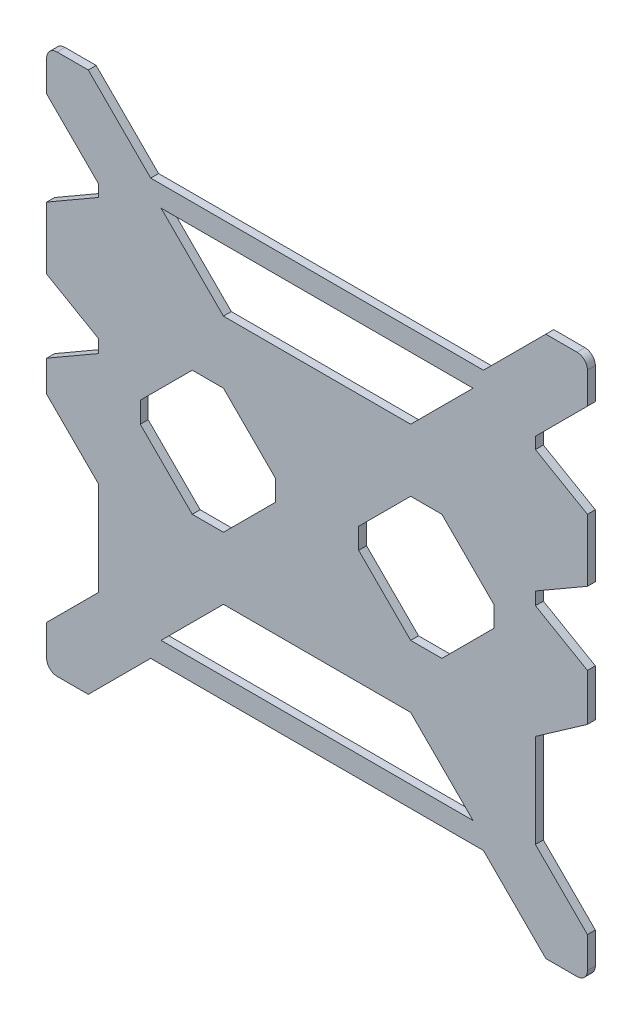
SolidWorks part; units mm, degrees
material "5052-H32"
ref_plane "Front Plane" through (0, 0, 0) normal (0, 0, 1) x (1, 0, 0)
ref_plane "Top Plane" through (0, 0, 0) normal (0, 1, 0) x (1, 0, 0)
ref_plane "Right Plane" through (0, 0, 0) normal (1, 0, 0) x (0, 0, -1)
sketch "Model" plane through (0, 0, 0) normal (0, 0, 1) x (1, 0, 0)
  line L0 (38.5361, 132.6139) -> (38.5361, 132.4727)
  line L1 (38.5361, -178.6774) -> (38.5361, -178.7219)
  line L2 (-253.5639, -197.5861) -> (-253.5639, -197.7273)
  line L3 (-290.6813, -31.2683) -> (-258.9313, -12.9374)
  line L4 (-258.9313, -82.0683) -> (-258.9313, -139.2183)
  line L5 (38.5361, 132.6139) -> (38.5361, 132.4727)
  line L6 (38.5361, -178.6774) -> (38.5361, -178.7219)
  line L7 (7.7687, -139.2183) -> (7.7687, -82.0683)
  line L8 (39.5187, -59.8367) -> (39.5187, -31.2683)
  line L9 (-23.9813, 95.7317) -> (-227.1813, 95.7317)
  line L10 (-290.6813, 108.4317) -> (-258.9313, 76.6817)
  line L11 (-30.3313, -145.5683) -> (-68.4313, -107.4683)
  line L12 (-23.9813, -158.2683) -> (14.1187, -196.3683)
  line L13 (39.5187, 108.4317) -> (39.5187, 127.4817)
  line L14 (-227.1813, 95.7317) -> (-265.2813, 133.8317)
  line L15 (-220.8313, 83.0317) -> (-182.7313, 44.9317)
  line L16 (-274.6813, -45.4288) -> (-254.6813, -45.4288) construction
  line L17 (39.5187, -170.9683) -> (7.7687, -139.2183)
  line L18 (-265.2813, -196.3683) -> (-227.1813, -158.2683)
  line L19 (-182.7313, -107.4683) -> (-68.4313, -107.4683)
  line L20 (-264.6813, -45.4288) -> (-264.6813, -43.5832) construction
  line L21 (7.7687, 76.6817) -> (39.5187, 108.4317)
  line L22 (-23.9813, 95.7317) -> (14.1187, 133.8317)
  line L23 (-30.3313, 83.0317) -> (-68.4313, 44.9317)
  line L24 (39.5187, -31.2683) -> (7.7687, -12.9374)
  line L25 (-258.9313, -139.2183) -> (-290.6813, -170.9683)
  line L26 (-182.7313, 44.9317) -> (-68.4313, 44.9317)
  line L27 (-220.8313, -145.5683) -> (-182.7313, -107.4683)
  line L28 (-220.8313, -145.5683) -> (-30.3313, -145.5683)
  line L29 (-258.9313, -82.0683) -> (-290.6813, -50.3183)
  line L30 (-290.6813, -31.2683) -> (-290.6813, -50.3183)
  line L31 (-274.6813, -43.9683) -> (-274.6813, -31.2683) construction
  line L32 (-258.9313, -12.9374) -> (-258.9313, -5.1492)
  line L33 (-201.7813, -69.3683) -> (-233.5313, -37.6183)
  line L34 (-182.7313, -69.3683) -> (-201.7813, -69.3683)
  line L35 (7.7687, -12.9374) -> (7.7687, -5.1492)
  line L36 (7.7687, -5.1492) -> (39.5187, 13.1817)
  line L37 (-150.9813, -37.6183) -> (-182.7313, -69.3683)
  line L38 (39.5187, -59.8367) -> (10.4646, -80.1806)
  line L39 (10.4646, -80.1806) -> (7.7687, -82.0683)
  line L40 (-100.1813, -37.6183) -> (-100.1813, -24.9183)
  line L41 (-150.9813, -37.6183) -> (-150.9813, -24.9183)
  line L42 (-150.9813, -24.9183) -> (-182.7313, 6.8317)
  line L43 (-182.7313, 6.8317) -> (-201.7813, 6.8317)
  line L44 (-201.7813, 6.8317) -> (-233.5313, -24.9183)
  line L45 (-233.5313, -24.9183) -> (-233.5313, -37.6183)
  line L46 (-17.6313, -24.9183) -> (-17.6313, -37.6183)
  line L47 (-49.3813, 6.8317) -> (-17.6313, -24.9183)
  line L48 (-220.8313, 83.0317) -> (-30.3313, 83.0317)
  line L49 (-68.4313, 6.8317) -> (-49.3813, 6.8317)
  line L50 (-100.1813, -24.9183) -> (-68.4313, 6.8317)
  line L51 (-100.1813, -37.6183) -> (-68.4313, -69.3683)
  line L52 (-68.4313, -69.3683) -> (-49.3813, -69.3683)
  line L53 (-49.3813, -69.3683) -> (-17.6313, -37.6183)
  line L54 (39.5187, 13.1817) -> (39.5187, 51.2817)
  line L55 (39.5187, 51.2817) -> (7.7687, 69.6126)
  line L56 (7.7687, 69.6126) -> (7.7687, 76.6817)
  line L57 (-258.9313, -5.1492) -> (-290.6813, 13.1817)
  line L58 (-265.2813, -196.3683) -> (-284.3313, -196.3683)
  line L59 (-290.6813, -190.0183) -> (-290.6813, -170.9683)
  line L60 (-290.6813, 108.4317) -> (-290.6813, 127.4817)
  line L61 (-284.3313, 133.8317) -> (-265.2813, 133.8317)
  line L62 (14.1187, 133.8317) -> (33.1687, 133.8317)
  line L63 (-290.6813, 13.1817) -> (-290.6813, 51.2817)
  line L64 (39.5187, -170.9683) -> (39.5187, -190.0183)
  line L65 (33.1687, -196.3683) -> (14.1187, -196.3683)
  line L66 (-258.9313, 76.6817) -> (-258.9313, 69.6126)
  line L67 (-258.9313, 69.6126) -> (-290.6813, 51.2817)
  line L68 (-274.6813, 30.5682) -> (-254.6813, 30.5682) construction
  line L69 (-254.6813, 30.5682) -> (23.5187, 30.5682) construction
  line L70 (23.5187, 30.5682) -> (23.5187, -45.4288) construction
  line L71 (-227.1813, -158.2683) -> (-23.9813, -158.2683)
  line L72 (38.5361, -178.6774) -> (38.5361, -178.7219)
  line L73 (3.5187, 30.5682) -> (3.5187, -45.4288) construction
  line L74 (-227.1813, -158.2683) -> (-23.9813, -158.2683)
  line L75 (38.5361, -178.6774) -> (38.5361, -178.7219)
  line L76 (-274.6813, 30.5682) -> (-274.6813, -45.4288) construction
  line L77 (-125.5813, 95.7317) -> (-125.5813, -158.2683) construction
  line L78 (-290.6813, -31.2683) -> (39.5187, -31.2683) construction
  arc A0 (33.1687, -196.3683) -> (39.5187, -190.0183) centre (33.1687, -190.0183) ccw
  arc A1 (-290.6813, -190.0183) -> (-284.3313, -196.3683) centre (-284.3313, -190.0183) ccw
  arc A2 (-290.6813, 127.4817) -> (-284.3313, 133.8317) centre (-284.3313, 127.4817) cw
  arc A3 (33.1687, 133.8317) -> (39.5187, 127.4817) centre (33.1687, 127.4817) cw
  circle A4 centre (-287.1253, -190.6025) radius 1.4605 construction
  circle A5 centre (33.7529, -190.6025) radius 1.4605 construction
  circle A6 centre (33.7529, 130.2757) radius 1.4605 construction
  circle A7 centre (-287.1253, 130.2757) radius 1.4605 construction
  circle A8 centre (-274.6813, -45.4288) radius 1.4605 construction
  circle A9 centre (-254.6813, -45.4288) radius 1.4605 construction
  circle A10 centre (23.5187, -45.4288) radius 1.4605 construction
  circle A11 centre (3.5187, -45.4288) radius 1.4605 construction
  circle A12 centre (23.5187, 30.5682) radius 1.4605 construction
  circle A13 centre (3.5187, 30.5682) radius 1.4605 construction
  circle A14 centre (-254.6813, 30.5682) radius 1.4605 construction
  circle A15 centre (-274.6813, 30.5682) radius 1.4605 construction
  circle A16 centre (-125.5813, -12.2183) radius 2 construction
  circle A17 centre (-125.5813, -50.3183) radius 2 construction
  point P72 (-125.5813, -31.2683)
  point P114 (-125.5813, 83.0317)
  point P120 (-233.5313, -31.2683)
  point P129 (-150.9813, -31.2683)
  point P149 (-125.5813, 44.9317)
  point P156 (-17.6313, -31.2683)
  dimension "D28" = 6.35
  dimension "D29" = 6.35
  dimension "D30" = 6.35
  dimension "D31" = 6.35
  dimension "D35" = 2.921
  dimension "D36" = 2.921
  dimension "D37" = 2.921
  dimension "D38" = 2.921
  dimension "D53" = 2.921
  dimension "D54" = 2.921
  dimension "D56" = 4
  dimension "D57" = 4
  dimension "D1" = 330.2
  dimension "D2" = 330.2
  dimension "D3" = 135
  dimension "D4" = 135
  dimension "D5" = 38.1
  dimension "D6" = 135
  dimension "D7" = 120
  dimension "D8" = 19.05
  dimension "D9" = 135
  dimension "D10" = 19.05
  dimension "D11" = 31.75
  dimension "D12" = 190.5
  dimension "D13" = 114.3
  dimension "D14" = 38.1
  dimension "D15" = 114.3
  dimension "D16" = 135
  dimension "D17" = 6.35
  dimension "D18" = 38.1
  dimension "D19" = 135
  dimension "D20" = 135
  dimension "D21" = 6.35
  dimension "D22" = 19.05
  dimension "D23" = 25.4
  dimension "D24" = 50.8
  dimension "D25" = 120
  dimension "D26" = 135
  dimension "D27" = 127
  dimension "D32" = 19.05
  dimension "D33" = 19.05
  dimension "D34" = 19.05
  dimension "D39" = 120
  dimension "D40" = 19.05
  dimension "D41" = 120
  dimension "D42" = 120
  dimension "D43" = 50.8
  dimension "D44" = 19.05
  dimension "D45" = 31.75
  dimension "D46" = 125
  dimension "D47" = 320.8782
  dimension "D48" = 320.8782
  dimension "D49" = 3.556
  dimension "D50" = 3.556
  dimension "D51" = 20
  dimension "D52" = 26
  dimension "D55" = 12.7
  dimension "D58" = 38.1
  dimension "D59" = 19.05
  dimension "D60" = 82.55
  dimension "D61" = 38.1
  dimension "D63" = 120
  dimension "D64" = 38.1
  dimension "D65" = 82.55
  dimension "D67" = 75.997
extrude "Boss-Extrude1" add sketch "Model" along normal mid plane 4.826
scale "Scale1" scale about centroid uniform scaling yes scale factor 0.666667
sketch "Sketch1" plane through (0, 0, 1.6087) normal (0, 0, 1) x (1, 0, 0)
  line L0 (23.5187, 30.5682) -> (23.5187, 17.7506) construction
  line L1 (-269.6813, -33.4288) -> (-259.6813, -33.4288)
  line L2 (-269.6813, -33.4288) -> (-269.6813, -57.4288)
  line L3 (-269.6813, -57.4288) -> (-259.6813, -57.4288)
  line L4 (-259.6813, -33.4288) -> (-259.6813, -57.4288)
  line L5 (-269.6813, 42.5712) -> (-259.6813, 42.5712)
  line L6 (-269.6813, 42.5712) -> (-269.6813, 18.5712)
  line L7 (-269.6813, 18.5712) -> (-259.6813, 18.5712)
  line L8 (-259.6813, 42.5712) -> (-259.6813, 18.5712)
  line L9 (8.5187, 42.5712) -> (18.5187, 42.5712)
  line L10 (8.5187, 42.5712) -> (8.5187, 18.5712)
  line L11 (8.5187, 18.5712) -> (18.5187, 18.5712)
  line L12 (18.5187, 42.5712) -> (18.5187, 18.5712)
  line L13 (8.5187, -33.4288) -> (18.5187, -33.4288)
  line L14 (8.5187, -33.4288) -> (8.5187, -57.4288)
  line L15 (8.5187, -57.4288) -> (18.5187, -57.4288)
  line L16 (18.5187, -33.4288) -> (18.5187, -57.4288)
  line L17 (39.5187, 13.1817) -> (39.5187, 51.2817) construction
  point P20 (13.5187, 42.5712)
  dimension "D3" = 12
  dimension "D4" = 5
  dimension "D5" = 10
  dimension "D8" = 100
  dimension "D11" = 100
  dimension "D15" = 12
  dimension "D17" = 16
  dimension "D1" = 10
  dimension "D2" = 24
  dimension "D6" = 24
  dimension "D7" = 5
  dimension "D9" = 24
  dimension "D10" = 5
  dimension "D12" = 10
  dimension "D13" = 10
  dimension "D14" = 24
  dimension "D16" = 5
extrude "Cut-Extrude1" [suppressed] cut sketch "Sketch1" against normal blind 10
sketch "Sketch2" plane through (0, 0, 1.6087) normal (0, 0, 1) x (1, 0, 0)
  line L0 (-21.4543, -133.1093) -> (-21.4543, 73.0617) construction
  line L1 (-21.4543, 73.0617) -> (-229.4543, 73.0617) construction
  line L2 (-229.4543, 73.0617) -> (-229.4543, -133.1093) construction
  line L3 (-229.4543, -133.1093) -> (-21.4543, -133.1093) construction
  line L4 (-235.5209, -30.263) -> (-15.3876, -30.263) construction
  line L7 (-125.4543, -140.3297) -> (-125.4543, 79.8037) construction
  line L10 (-235.5209, -140.3297) -> (-235.5209, 79.8037) construction
  line L11 (-235.5209, 79.8037) -> (-15.3876, 79.8037) construction
  line L12 (-15.3876, 79.8037) -> (-15.3876, -140.3297) construction
  line L13 (-15.3876, -140.3297) -> (-235.5209, -140.3297) construction
  circle A0 centre (-229.4543, -133.1093) radius 1.5
  circle A1 centre (-229.4543, 73.0617) radius 1.5
  circle A2 centre (-21.4543, 73.0617) radius 1.5
  circle A3 centre (-21.4543, -133.1093) radius 1.5
  dimension "D1" = 3
  dimension "D2" = 208
  dimension "D3" = 104
